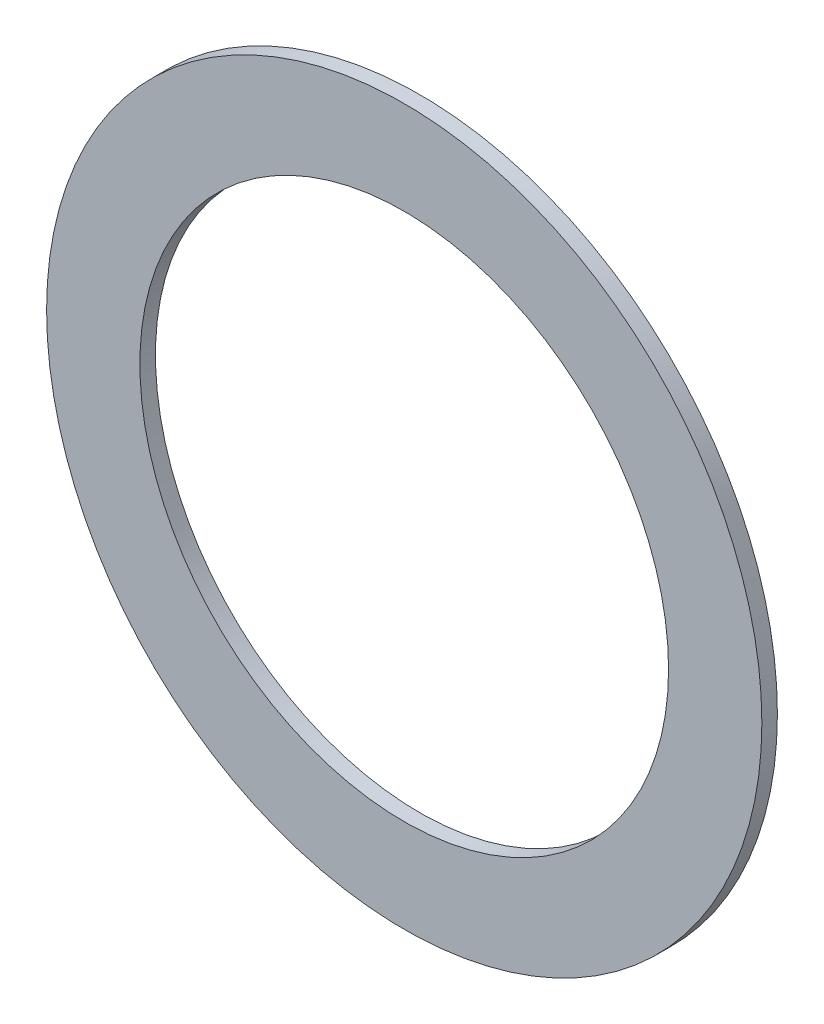
SolidWorks part; units mm, degrees
ref_plane "Přední rovina" through (0, 0, 0) normal (0, 0, 1) x (1, 0, 0)
ref_plane "Horní rovina" through (0, 0, 0) normal (0, 1, 0) x (1, 0, 0)
ref_plane "Pravá rovina" through (0, 0, 0) normal (1, 0, 0) x (0, 0, -1)
sketch "Skica1" plane through (0, 0, 0) normal (0, 0, 1) x (1, 0, 0)
  circle A0 centre (0, 0) radius 34
  circle A1 centre (0, 0) radius 46
  dimension "D1" = 68
  dimension "D2" = 92
extrude "Přidat vysunutím1" add sketch "Skica1" along normal blind 2
sketch "Skica2" plane through (0, 0, 0) normal (0, 0, -1) x (-1, 0, 0)
  line L0 (0, 0) -> (0, 46) construction
  line L1 (0, 0) -> (-46, 0) construction
  line L2 (0, 0) -> (0, -46) construction
  line L3 (0, 0) -> (46, 0) construction
  line L4 (-45.6087, 5.9872) -> (45.6087, -5.9872) construction
  line L5 (5.9872, 45.6087) -> (-5.9872, -45.6087) construction
  circle A0 centre (0, 0) radius 46 construction
  circle A1 centre (0, 0) radius 34 construction
  arc A2 (-33.7108, 4.4253) -> (0, 34) centre (0, 0) cw
  arc A3 (4.4253, 33.7108) -> (34, 0) centre (0, 0) cw
  arc A4 (33.7108, -4.4253) -> (0, -34) centre (0, 0) cw
  arc A5 (-4.4253, -33.7108) -> (-34, 0) centre (0, 0) cw
  arc A6 (-45.6087, 5.9872) -> (0, 46) centre (0, 0) cw
  arc A7 (5.9872, 45.6087) -> (46, 0) centre (0, 0) cw
  arc A8 (45.6087, -5.9872) -> (0, -46) centre (0, 0) cw
  arc A9 (-5.9872, -45.6087) -> (-46, 0) centre (0, 0) cw
  point P12 (-33.7108, 4.4253)
  point P13 (-34, 0)
  point P16 (0, 34)
  point P17 (4.4253, 33.7108)
  point P18 (34, 0)
  point P19 (33.7108, -4.4253)
  point P20 (0, -34)
  point P21 (-4.4253, -33.7108)
  dimension "D1" = 6
  dimension "D2" = 6
